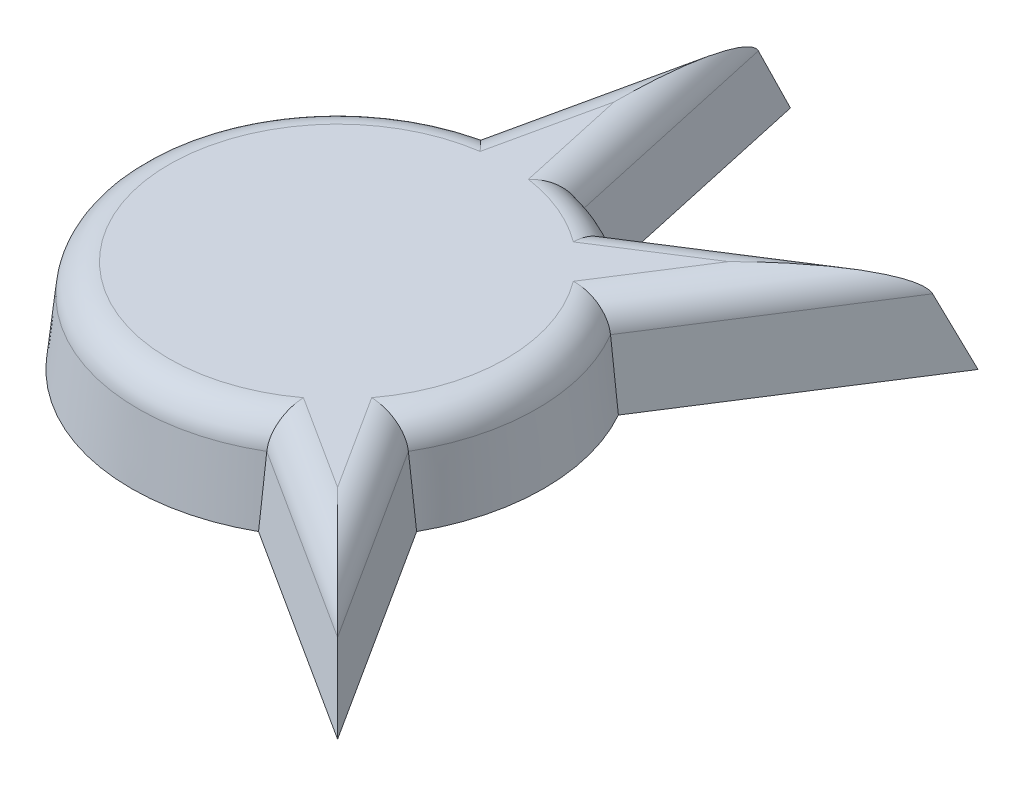
SolidWorks part; units mm, degrees
material "ABS"
ref_plane "Front Plane" through (0, 0, 0) normal (0, 0, 1) x (1, 0, 0)
ref_plane "Top Plane" through (0, 0, 0) normal (0, 1, 0) x (1, 0, 0)
ref_plane "Right Plane" through (0, 0, 0) normal (1, 0, 0) x (0, 0, -1)
sketch "Sketch1" plane through (0, 0, 0) normal (0, 1, 0) x (1, 0, 0)
  line L1 (-17.5, 17.5) -> (17.5, 17.5)
  line L2 (-17.5, 17.5) -> (-17.5, -17.5)
  line L3 (-17.5, -17.5) -> (17.5, -17.5)
  line L4 (17.5, 17.5) -> (17.5, -17.5)
  line L5 (-17.5, 17.5) -> (17.5, -17.5) construction
  line L6 (-17.5, -17.5) -> (17.5, 17.5) construction
  point P0 (0, 0)
  dimension "D1" = 35
sketch "Sketch2" plane through (0, 0, 0) normal (0, 1, 0) x (1, 0, 0)
  line L0 (0, 14.5436) -> (-1.795, 6.3768)
  line L1 (0, 14.5436) -> (0, 6.6246) construction
  line L2 (0, 14.5436) -> (1.795, 6.3768)
  line L3 (10.2839, 10.2839) -> (3.2399, 5.7783)
  line L4 (10.2839, 10.2839) -> (5.7783, 3.2399)
  line L7 (10.2839, -10.2839) -> (5.7783, -3.2399)
  line L8 (10.2839, -10.2839) -> (3.2399, -5.7783)
  line L17 (14.5436, 0) -> (6.3768, -1.795) [skipped]
  line L18 (14.5436, 0) -> (6.3768, 1.795) [skipped]
  line L19 (-10.2839, 10.2839) -> (-3.2399, 5.7783) [skipped]
  line L20 (-10.2839, 10.2839) -> (-5.7783, 3.2399) [skipped]
  line L21 (-14.5436, 0) -> (-6.3768, 1.795) [skipped]
  line L22 (-14.5436, 0) -> (-6.3768, -1.795) [skipped]
  line L23 (-10.2839, -10.2839) -> (-5.7783, -3.2399) [skipped]
  line L24 (-10.2839, -10.2839) -> (-3.2399, -5.7783) [skipped]
  line L25 (0, -14.5436) -> (-1.795, -6.3768) [skipped]
  line L26 (0, -14.5436) -> (1.795, -6.3768) [skipped]
  circle A0 centre (0, 0) radius 6.6246
  point P31 (0, 0)
  dimension "D1" = 8
extrude "Boss-Extrude1" add sketch "Sketch2" along normal blind 3 draft 6
fillet "Fillet1" radius 1 9 edges at (-5.8291, 3, 2.4145) (-0.7641, 3, -9.5981) (0.7641, 3, -9.5981) (2.4145, 3, -5.8291) (6.2466, 3, -7.3272) (7.3272, 3, -6.2466) (6.3093, 3, 0) (7.3272, 3, 6.2466) (6.2466, 3, 7.3272)
